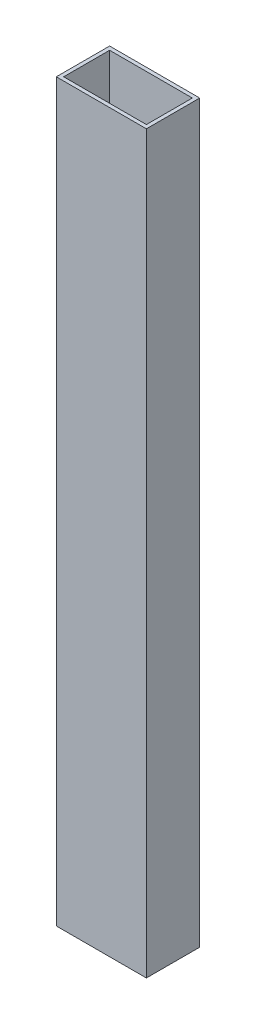
SolidWorks part; units mm, degrees
ref_plane "Alzado" through (0, 0, 0) normal (0, 0, 1) x (1, 0, 0)
ref_plane "Planta" through (0, 0, 0) normal (0, 1, 0) x (1, 0, 0)
ref_plane "Vista lateral" through (0, 0, 0) normal (1, 0, 0) x (0, 0, -1)
sketch "Croquis2" plane through (0, 0, 0) normal (0, 1, 0) x (1, 0, 0)
  line L9 (-22.5, 12.5) -> (22.5, 12.5)
  line L10 (-22.5, 12.5) -> (-22.5, -12.5)
  line L11 (-22.5, -12.5) -> (22.5, -12.5)
  line L12 (22.5, 12.5) -> (22.5, -12.5)
  line L13 (-22.5, 12.5) -> (22.5, -12.5) construction
  line L14 (-22.5, -12.5) -> (22.5, 12.5) construction
  line L15 (-24.5, 14.5) -> (24.5, 14.5)
  line L16 (-24.5, 14.5) -> (-24.5, -14.5)
  line L17 (-24.5, -14.5) -> (24.5, -14.5)
  line L18 (24.5, 14.5) -> (24.5, -14.5)
  line L19 (-24.5, 14.5) -> (24.5, -14.5) construction
  line L20 (-24.5, -14.5) -> (24.5, 14.5) construction
  point P0 (0, 0)
  point P5 (0, 0)
  dimension "D1" = 25
  dimension "D2" = 45
  dimension "D3" = 2
  dimension "D4" = 2
extrude "Saliente-Extruir2" add sketch "Croquis2" along normal mid plane 400
